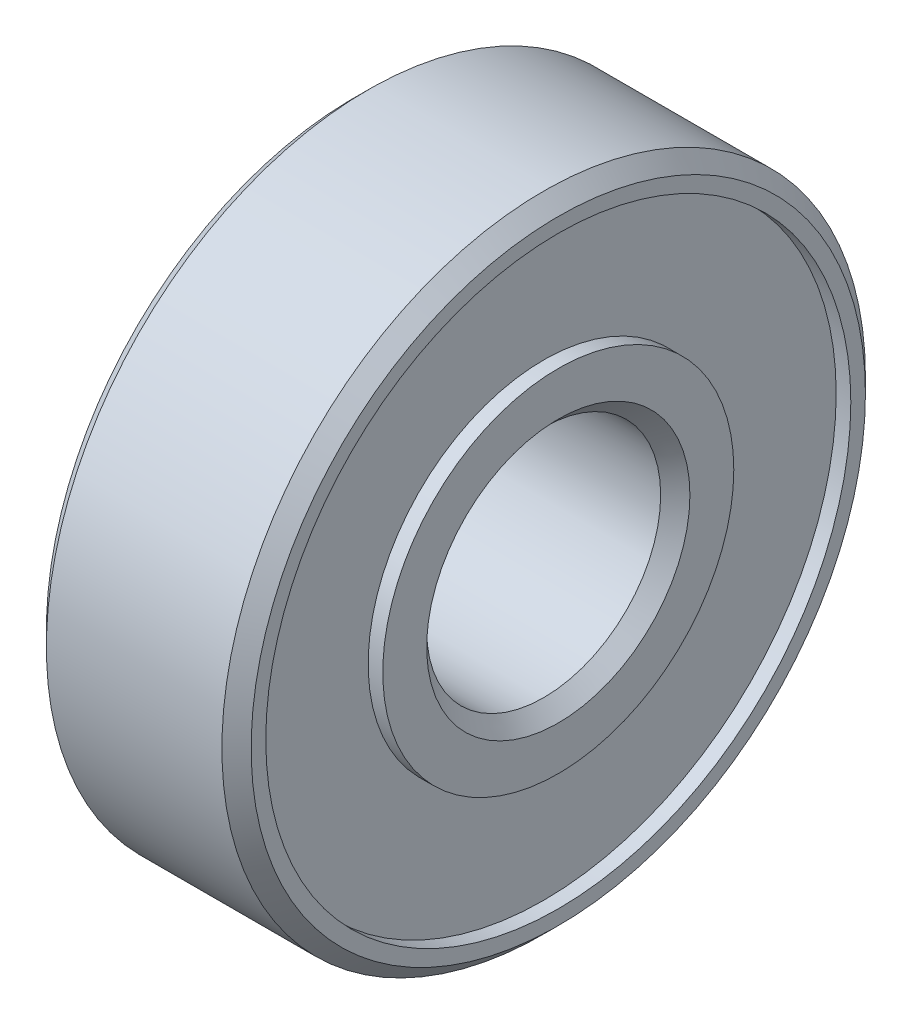
SolidWorks part; units mm, degrees
ref_plane "Plan de face" through (0, 0, 0) normal (0, 0, 1) x (1, 0, 0)
ref_plane "Plan de dessus" through (0, 0, 0) normal (0, 1, 0) x (1, 0, 0)
ref_plane "Plan de droite" through (0, 0, 0) normal (1, 0, 0) x (0, 0, -1)
sketch "Esquisse1" plane through (0, 0, 0) normal (0, 0, 1) x (1, 0, 0)
  line L0 (-3, 11) -> (3, 11)
  line L1 (3.5, 10.5) -> (3.5, 10)
  line L2 (3.5, 10) -> (3, 10)
  line L3 (3, 10) -> (3, 6)
  line L4 (3, 6) -> (3.5, 6)
  line L5 (3.5, 6) -> (3.5, 4.5)
  line L6 (3, 4) -> (-3, 4)
  line L7 (-3.5, 4.5) -> (-3.5, 6)
  line L8 (-3.5, 6) -> (-3, 6)
  line L9 (-3, 6) -> (-3, 10)
  line L10 (-3, 10) -> (-3.5, 10)
  line L11 (-3.5, 10) -> (-3.5, 10.5)
  line L12 (-3.5, 10.5) -> (-3, 11)
  line L13 (3, 11) -> (3.5, 10.5)
  line L14 (-3, 4) -> (-3.5, 4.5)
  line L15 (3.5, 4.5) -> (3, 4)
  line L16 (0, 0) -> (-50000, 0) construction
  point P0 (-3.5, 11)
  point P1 (3.5, 11)
  point P7 (3.5, 4)
  point P8 (-3.5, 4)
  dimension "D1" = 7
  dimension "D2" = 4
  dimension "D3" = 2
  dimension "D4" = 1
  dimension "D5" = 11
  dimension "D6" = 0.5
  dimension "D7" = 0.5
revolve "Révolution1" add sketch "Esquisse1" angle 360 about L16
